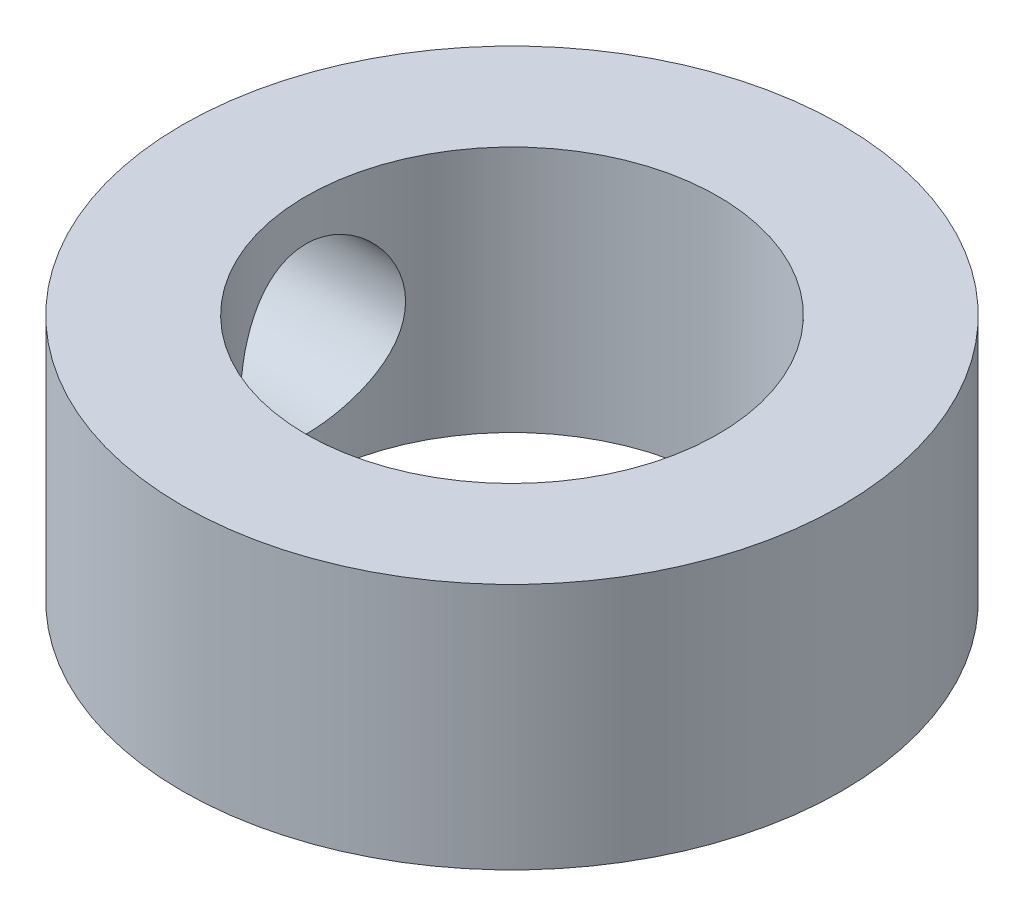
SolidWorks part; units mm, degrees
ref_plane "Front Plane" through (0, 0, 0) normal (0, 0, 1) x (1, 0, 0)
ref_plane "Top Plane" through (0, 0, 0) normal (0, 1, 0) x (1, 0, 0)
ref_plane "Right Plane" through (0, 0, 0) normal (1, 0, 0) x (0, 0, -1)
sketch "Sketch1" plane through (0, 0, 0) normal (0, 1, 0) x (1, 0, 0)
  circle A0 centre (0, 0) radius 2.5
  circle A1 centre (0, 0) radius 4
extrude "Boss-Extrude1" add sketch "Sketch1" along normal blind 3
sketch "Sketch2" plane through (0, 0, 0) normal (1, 0, 0) x (0, 0, -1)
  line L0 (0, 0) -> (0, 3) construction
  circle A0 centre (0, 1.5) radius 1
extrude "Cut-Extrude1" cut sketch "Sketch2" against normal blind 13
